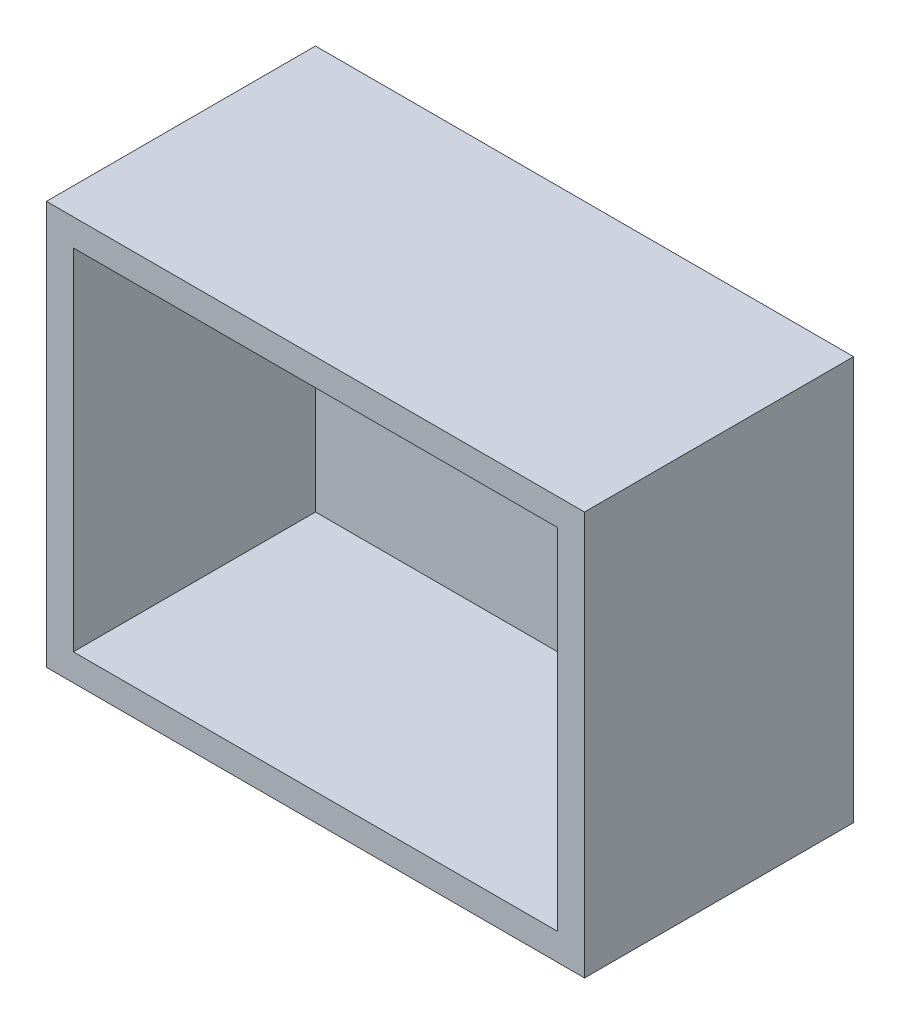
SolidWorks part; units mm, degrees
ref_plane "前视基准面" through (0, 0, 0) normal (0, 0, 1) x (1, 0, 0)
ref_plane "上视基准面" through (0, 0, 0) normal (0, 1, 0) x (1, 0, 0)
ref_plane "右视基准面" through (0, 0, 0) normal (1, 0, 0) x (0, 0, -1)
other "Configuration Table"
sketch "草图1" plane through (0, 0, 0) normal (0, 0, 1) x (1, 0, 0)
  line L1 (-14.6255, 27.5183) -> (25.3745, 27.5183)
  line L2 (-14.6255, 27.5183) -> (-14.6255, -2.4817)
  line L3 (-14.6255, -2.4817) -> (25.3745, -2.4817)
  line L4 (25.3745, 27.5183) -> (25.3745, -2.4817)
  dimension "D1" = 30
  dimension "D2" = 40
extrude "凸台-拉伸1" add sketch "草图1" along normal blind 20
sketch "草图2" plane through (0, 0, 20) normal (0, 0, 1) x (1, 0, 0)
  line L0 (-12.6255, 25.5183) -> (-12.6255, -0.4817)
  line L1 (-14.6255, 27.5183) -> (25.3745, 27.5183) construction
  line L2 (-14.6255, 27.5183) -> (-14.6255, -2.4817) construction
  line L3 (-14.6255, -2.4817) -> (25.3745, -2.4817) construction
  line L4 (25.3745, 27.5183) -> (25.3745, -2.4817) construction
  line L5 (-12.6255, -0.4817) -> (23.3745, -0.4817)
  line L6 (23.3745, 25.5183) -> (23.3745, -0.4817)
  line L7 (-12.6255, 25.5183) -> (23.3745, 25.5183)
  dimension "D1" = 2
extrude "切除-拉伸2" cut sketch "草图2" against normal blind 18 contours L7 L0 L5 L6 | L2 L1 L4 L3
